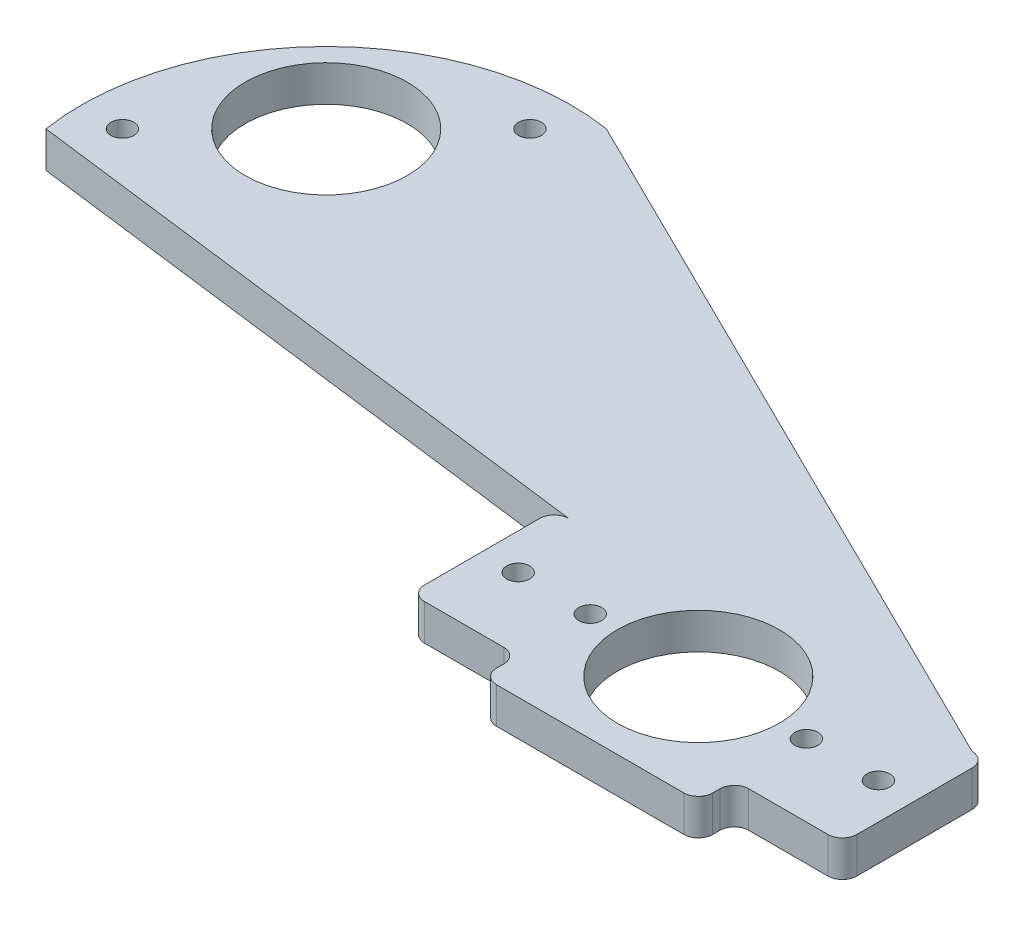
SolidWorks part; units mm, degrees
material "PC High Viscosity"
ref_plane "Front Plane" through (0, 0, 0) normal (0, 0, 1) x (1, 0, 0)
ref_plane "Top Plane" through (0, 0, 0) normal (0, 1, 0) x (1, 0, 0)
ref_plane "Right Plane" through (0, 0, 0) normal (1, 0, 0) x (0, 0, -1)
sketch "Sketch1" plane through (0, 0, 0) normal (0, 1, 0) x (1, 0, 0)
  line L0 (0, -55) -> (0, 55) construction
  line L1 (-16.51, -19.05) -> (16.51, -19.05)
  line L2 (-19.05, -16.51) -> (-19.05, -15.24)
  line L3 (-16.51, 19.05) -> (16.51, 19.05)
  line L4 (19.05, -16.51) -> (19.05, -15.24)
  line L5 (-19.05, -19.05) -> (19.05, 19.05) construction
  line L6 (-19.05, 19.05) -> (19.05, -19.05) construction
  line L7 (-21.59, 12.7) -> (-35.56, 12.7)
  line L9 (-21.59, -12.7) -> (-35.56, -12.7)
  line L10 (-38.1, 10.16) -> (-38.1, -10.16)
  line L11 (21.59, -12.7) -> (35.56, -12.7)
  line L12 (38.1, 10.16) -> (38.1, -10.16)
  line L13 (21.59, 12.7) -> (35.56, 12.7)
  line L15 (-19.05, 15.24) -> (-19.05, 16.51)
  line L16 (19.05, 15.24) -> (19.05, 16.51)
  line L17 (-24.384, 18.034) -> (-24.384, 12.7)
  line L18 (-18.034, 24.384) -> (18.034, 24.384)
  line L19 (24.384, 18.034) -> (24.384, 12.7)
  line L20 (-55, 0) -> (55, 0) construction
  line L21 (24.384, -18.034) -> (24.384, -12.7)
  line L22 (-24.384, -18.034) -> (-24.384, -12.7)
  line L23 (-18.034, -24.384) -> (18.034, -24.384)
  circle A0 centre (0, 0) radius 14.2875
  circle A1 centre (-31.75, 0) radius 2.0193
  circle A2 centre (-19.05, 0) radius 2.0193
  circle A3 centre (19.05, 0) radius 2.0193
  circle A4 centre (31.75, 0) radius 2.0193
  arc A5 (-19.05, 16.51) -> (-16.51, 19.05) centre (-16.51, 16.51) cw
  arc A6 (-19.05, 15.24) -> (-21.59, 12.7) centre (-21.59, 15.24) cw
  arc A7 (-35.56, 12.7) -> (-38.1, 10.16) centre (-35.56, 10.16) ccw
  arc A8 (-38.1, -10.16) -> (-35.56, -12.7) centre (-35.56, -10.16) ccw
  arc A9 (-19.05, -15.24) -> (-21.59, -12.7) centre (-21.59, -15.24) ccw
  arc A10 (-19.05, -16.51) -> (-16.51, -19.05) centre (-16.51, -16.51) ccw
  arc A11 (19.05, 16.51) -> (16.51, 19.05) centre (16.51, 16.51) ccw
  arc A12 (21.59, 12.7) -> (19.05, 15.24) centre (21.59, 15.24) cw
  arc A13 (38.1, 10.16) -> (35.56, 12.7) centre (35.56, 10.16) ccw
  arc A14 (19.05, -16.51) -> (16.51, -19.05) centre (16.51, -16.51) cw
  arc A15 (38.1, -10.16) -> (35.56, -12.7) centre (35.56, -10.16) cw
  arc A16 (21.59, -12.7) -> (19.05, -15.24) centre (21.59, -15.24) ccw
  circle A18 centre (-18.034, 18.034) radius 1.9939
  arc A19 (-24.384, 18.034) -> (-18.034, 24.384) centre (-18.034, 18.034) cw
  circle A20 centre (18.034, 18.034) radius 1.9939
  arc A21 (24.384, 18.034) -> (18.034, 24.384) centre (18.034, 18.034) ccw
  circle A22 centre (18.034, -18.034) radius 1.9939
  circle A23 centre (-18.034, -18.034) radius 1.9939
  arc A24 (-24.384, -18.034) -> (-18.034, -24.384) centre (-18.034, -18.034) ccw
  arc A25 (24.384, -18.034) -> (18.034, -24.384) centre (18.034, -18.034) cw
  point P30 (-19.05, 12.7)
  point P33 (-38.1, 12.7)
  point P36 (-38.1, -12.7)
  point P39 (-19.05, -12.7)
  point P48 (19.05, 12.7)
  point P51 (38.1, 12.7)
  point P57 (38.1, -12.7)
  point P60 (19.05, -12.7)
  point P72 (0, 24.384)
  point P84 (0, -24.384)
  dimension "D1" = 28.575
  dimension "D8" = 4.0386
  dimension "D9" = 4.0386
  dimension "D11" = 2.54
  dimension "D16" = 6.35
  dimension "D17" = 3.9878
  dimension "D2" = 38.1
  dimension "D3" = 38.1
  dimension "D4" = 25.4
  dimension "D5" = 38.1
  dimension "D6" = 6.35
  dimension "D7" = 19.05
  dimension "D10" = 12.7
  dimension "D13" = 18.034
  dimension "D15" = 18.034
extrude "Boss-Extrude1" add sketch "Sketch1" along normal blind 6.35 contours L2 A23 L1 A22 L4 A16 L11 A15 L12 A13 L13 A12 L16 A20 L3 A18 L15 A6 L7 A7 L10 A8 L9 A9 A3 A2 A1 A0 A4 | L15 A18 L3 A5 | A20 L16 A11 L3 | L4 A22 L1 A14 | A23 L2 A10 L1
sketch "Sketch2" [suppressed] plane through (0, 0, 0) normal (0, 0, 1) x (1, 0, 0)
  line L1 (-16.51, -19.05) -> (16.51, -19.05)
  line L2 (-19.05, -16.51) -> (-19.05, -15.24)
  line L3 (-16.51, 19.05) -> (16.51, 19.05)
  line L4 (19.05, -16.51) -> (19.05, -15.24)
  line L5 (-19.05, -19.05) -> (19.05, 19.05) construction
  line L6 (-19.05, 19.05) -> (19.05, -19.05) construction
  line L7 (-21.59, 12.7) -> (-35.56, 12.7)
  line L9 (-21.59, -12.7) -> (-35.56, -12.7)
  line L10 (-38.1, 10.16) -> (-38.1, -10.16)
  line L11 (21.59, -12.7) -> (35.56, -12.7)
  line L12 (38.1, 10.16) -> (38.1, -10.16)
  line L13 (21.59, 12.7) -> (35.56, 12.7)
  line L15 (-19.05, 15.24) -> (-19.05, 16.51)
  line L16 (19.05, 15.24) -> (19.05, 16.51)
  line L17 (-24.384, 18.034) -> (-24.384, 12.7)
  line L18 (-18.034, 24.384) -> (18.034, 24.384)
  line L19 (24.384, 18.034) -> (24.384, 12.7)
  line L21 (24.384, -18.034) -> (24.384, -12.7)
  line L22 (-24.384, -18.034) -> (-24.384, -12.7)
  line L23 (-18.034, -24.384) -> (18.034, -24.384)
  line L24 (-35.56, 12.7) -> (-24.384, 12.7) construction
  line L25 (-24.384, 12.7) -> (-24.384, 18.034) construction
  circle A0 centre (0, 0) radius 14.2875
  circle A1 centre (-31.75, 0) radius 2.0193
  circle A2 centre (-19.05, 0) radius 2.0193
  circle A3 centre (19.05, 0) radius 2.0193
  circle A4 centre (31.75, 0) radius 2.0193
  arc A5 (-19.05, 16.51) -> (-16.51, 19.05) centre (-16.51, 16.51) cw
  arc A6 (-19.05, 15.24) -> (-21.59, 12.7) centre (-21.59, 15.24) cw
  arc A7 (-35.56, 12.7) -> (-38.1, 10.16) centre (-35.56, 10.16) ccw
  arc A8 (-38.1, -10.16) -> (-35.56, -12.7) centre (-35.56, -10.16) ccw
  arc A9 (-19.05, -15.24) -> (-21.59, -12.7) centre (-21.59, -15.24) ccw
  arc A10 (-19.05, -16.51) -> (-16.51, -19.05) centre (-16.51, -16.51) ccw
  arc A11 (19.05, 16.51) -> (16.51, 19.05) centre (16.51, 16.51) ccw
  arc A12 (21.59, 12.7) -> (19.05, 15.24) centre (21.59, 15.24) cw
  arc A13 (38.1, 10.16) -> (35.56, 12.7) centre (35.56, 10.16) ccw
  arc A14 (19.05, -16.51) -> (16.51, -19.05) centre (16.51, -16.51) cw
  arc A15 (38.1, -10.16) -> (35.56, -12.7) centre (35.56, -10.16) cw
  arc A16 (21.59, -12.7) -> (19.05, -15.24) centre (21.59, -15.24) ccw
  circle A18 centre (-18.034, 18.034) radius 1.9939
  arc A19 (-24.384, 18.034) -> (-18.034, 24.384) centre (-18.034, 18.034) cw
  circle A20 centre (18.034, 18.034) radius 1.9939
  arc A21 (24.384, 18.034) -> (18.034, 24.384) centre (18.034, 18.034) ccw
  circle A22 centre (18.034, -18.034) radius 1.9939
  circle A23 centre (-18.034, -18.034) radius 1.9939
  arc A24 (-24.384, -18.034) -> (-18.034, -24.384) centre (-18.034, -18.034) ccw
  arc A25 (24.384, -18.034) -> (18.034, -24.384) centre (18.034, -18.034) cw
  spline S0 degree 2 poles (-35.56, 12.7) (-24.384, 12.7) (-24.384, 18.034) knots 0 0 0 1 1 1
  point P30 (-19.05, 12.7)
  point P33 (-38.1, 12.7)
  point P36 (-38.1, -12.7)
  point P39 (-19.05, -12.7)
  point P48 (19.05, 12.7)
  point P51 (38.1, 12.7)
  point P57 (38.1, -12.7)
  point P60 (19.05, -12.7)
  point P72 (0, 24.384)
  point P84 (0, -24.384)
  dimension "D1" = 28.575
  dimension "D8" = 4.0386
  dimension "D9" = 4.0386
  dimension "D11" = 2.54
  dimension "D16" = 6.35
  dimension "D17" = 3.9878
  dimension "D2" = 38.1
  dimension "D3" = 38.1
  dimension "D4" = 25.4
  dimension "D5" = 38.1
  dimension "D6" = 6.35
  dimension "D7" = 19.05
  dimension "D10" = 12.7
  dimension "D13" = 18.034
  dimension "D15" = 18.034
extrude "Boss-Extrude2" [suppressed] add sketch "Sketch2" against normal blind 3.175 contours L2 A23 L1 A22 L4 A16 L11 A15 L12 A13 L13 A12 L16 A20 L3 A18 L15 A6 L7 A7 L10 A8 L9 A9 A3 A2 A1 A0 A4 | L19 A21 L18 A19 L17 L7 A6 L15 A18 L3 A20 L16 A12 L13 | A25 L21 L11 A16 L4 A22 L1 A23 L2 A9 L9 L22 A24 L23
sketch "Sketch3" plane through (0, 6.35, 0) normal (0, 1, 0) x (1, 0, 0)
  line L0 (-141.0931, 26.1043) -> (-91.7017, 75.4957) construction
  line L1 (-130.6849, 50.8) -> (-102.1099, 50.8) construction
  line L2 (-116.3974, 50.8) -> (-44.0148, 68.7605) construction
  line L3 (-141.0931, 26.1043) -> (-35.56, 12.7)
  line L7 (-91.7017, 75.4957) -> (35.56, 12.7)
  circle A0 centre (-116.3974, 50.8) radius 14.2875
  circle A1 centre (-31.75, 0) radius 2.0193 construction
  circle A2 centre (-134.3579, 32.8395) radius 2.0193
  circle A3 centre (-98.4369, 68.7605) radius 2.0193
  arc A5 (-141.0931, 26.1043) -> (-91.7017, 75.4957) centre (-98.4369, 32.8395) cw
  point P7 (-116.3974, 50.8)
  point P15 (0, 0)
  point P18 (0, 0)
  point P19 (0, 0)
  point P20 (-90.3432, 50.8)
  dimension "D1" = 43.1847
  dimension "D3" = 28.575
  dimension "D7" = 4.0386
  dimension "D8" = 4.0386
  dimension "D9" = 69.85
  dimension "D10" = 127
  dimension "D2" = 50.8
  dimension "D4" = 45
  dimension "D5" = 25.4
  dimension "D6" = 25.4
extrude "Boss-Extrude3" add sketch "Sketch3" against normal blind 6.35
